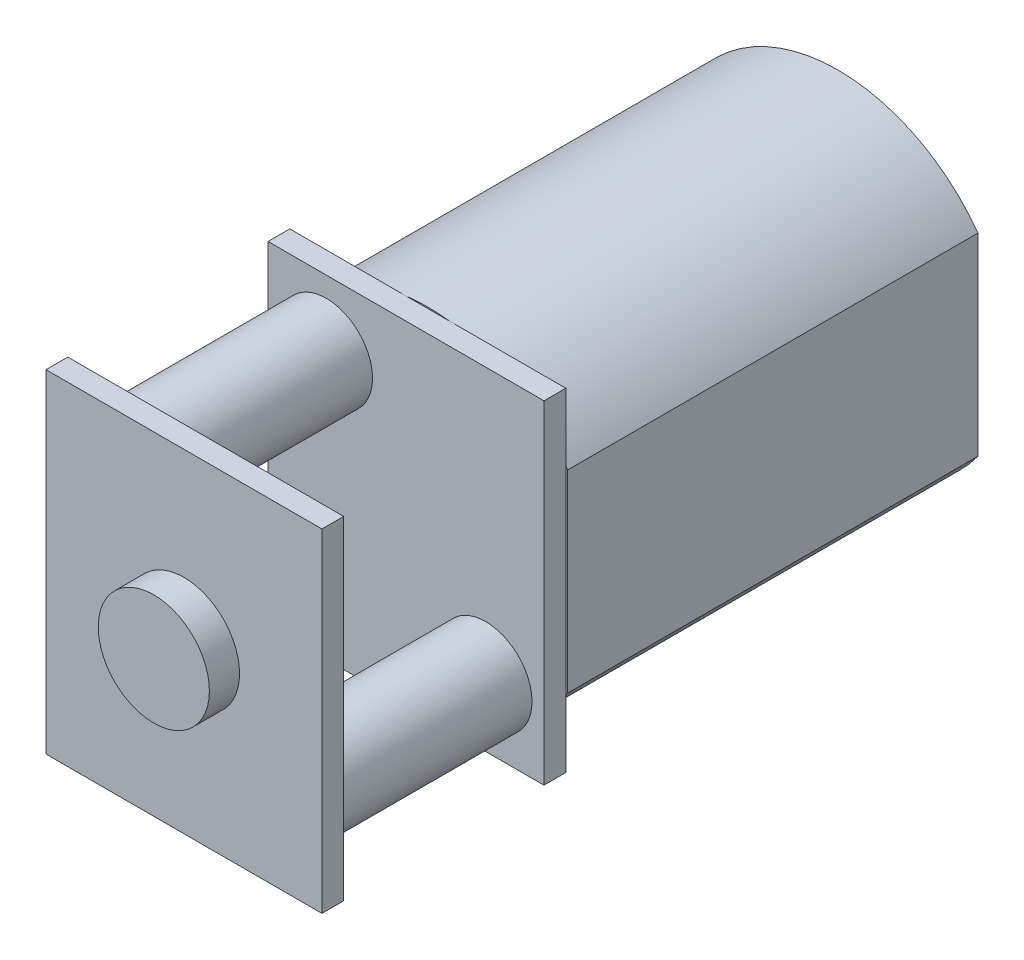
SolidWorks part; units mm, degrees
ref_plane "Plan de face" through (0, 0, 0) normal (0, 0, 1) x (1, 0, 0)
ref_plane "Plan de dessus" through (0, 0, 0) normal (0, 1, 0) x (1, 0, 0)
ref_plane "Plan de droite" through (0, 0, 0) normal (1, 0, 0) x (0, 0, -1)
sketch "Esquisse1" plane through (0, 0, 0) normal (0, 0, 1) x (1, 0, 0)
  line L2 (0, 0) -> (0, 6.92)
  line L4 (10.02, 0) -> (10.02, 6.92)
  arc A0 (0, 6.92) -> (10.02, 6.92) centre (5.01, 3.2734) cw
  arc A1 (0, 0) -> (10.02, 0) centre (5.01, 3.6466) ccw
  dimension "D3" = 6.1966
  dimension "D4" = 6.1966
  dimension "D1" = 10.02
  dimension "D2" = 6.92
extrude "Boss.-Extru.2" add sketch "Esquisse1" along normal blind 14.69
sketch "Esquisse2" plane through (0, 0, 14.69) normal (0, 0, 1) x (1, 0, 0)
  line L0 (0, 3.46) -> (10.02, 3.46) construction
  line L1 (0, 6.92) -> (0, 0) construction
  line L2 (10.02, 0) -> (10.02, 6.92) construction
  line L3 (5.01, 9.47) -> (5.01, -2.55) construction
  line L5 (0.07, -2.5) -> (9.95, -2.5)
  line L6 (0.07, -2.5) -> (0.07, 9.42)
  line L7 (0.07, 9.42) -> (9.95, 9.42)
  line L8 (9.95, -2.5) -> (9.95, 9.42)
  line L9 (0.07, -2.5) -> (9.95, 9.42) construction
  line L10 (0.07, 9.42) -> (9.95, -2.5) construction
  arc A0 (10.02, 6.92) -> (0, 6.92) centre (5.01, 3.2734) ccw construction
  arc A1 (0, 0) -> (10.02, 0) centre (5.01, 3.6466) ccw construction
  point P14 (5.01, 3.46)
  dimension "D1" = 11.92
  dimension "D2" = 9.88
extrude "Boss.-Extru.3" add sketch "Esquisse2" along normal blind 0.78
sketch "Esquisse3" plane through (0, 0, 15.47) normal (0, 0, 1) x (1, 0, 0)
  line L0 (9.95, -0.125) -> (7.865, -0.125) construction
  line L1 (7.865, 9.42) -> (7.865, -0.125) construction
  line L2 (9.95, 9.42) -> (0.07, 9.42) construction
  line L3 (9.95, -2.5) -> (9.95, 9.42) construction
  line L4 (2.155, 7.045) -> (2.155, -2.5) construction
  line L5 (0.07, 7.045) -> (2.155, 7.045) construction
  line L6 (0.07, 9.42) -> (0.07, -2.5) construction
  line L7 (0.07, -2.5) -> (9.95, -2.5) construction
  circle A0 centre (7.865, -0.125) radius 1.655
  circle A1 centre (2.155, 7.045) radius 1.655
  dimension "D3" = 9.545
  dimension "D5" = 3.31
  dimension "D6" = 3.31
  dimension "D1" = 9.545
  dimension "D2" = 2.085
  dimension "D4" = 2.085
extrude "Boss.-Extru.4" add sketch "Esquisse3" along normal blind 7.17
sketch "Esquisse4" plane through (0, 0, 22.64) normal (0, 0, 1) x (1, 0, 0)
  line L3 (0.07, -2.5) -> (9.95, -2.5)
  line L4 (0.07, -2.5) -> (0.07, 9.42)
  line L5 (0.07, 9.42) -> (9.95, 9.42)
  line L6 (9.95, -2.5) -> (9.95, 9.42)
  point P8 (5.01, 3.46)
  dimension "D1" = 11.92
  dimension "D2" = 9.88
extrude "Boss.-Extru.5" add sketch "Esquisse4" along normal blind 0.78
sketch "Esquisse5" plane through (0, 0, 23.42) normal (0, 0, 1) x (1, 0, 0)
  circle A0 centre (5.01, 3.46) radius 1.99
  dimension "D1" = 3.98
extrude "Boss.-Extru.6" add sketch "Esquisse5" along normal blind 1.08
